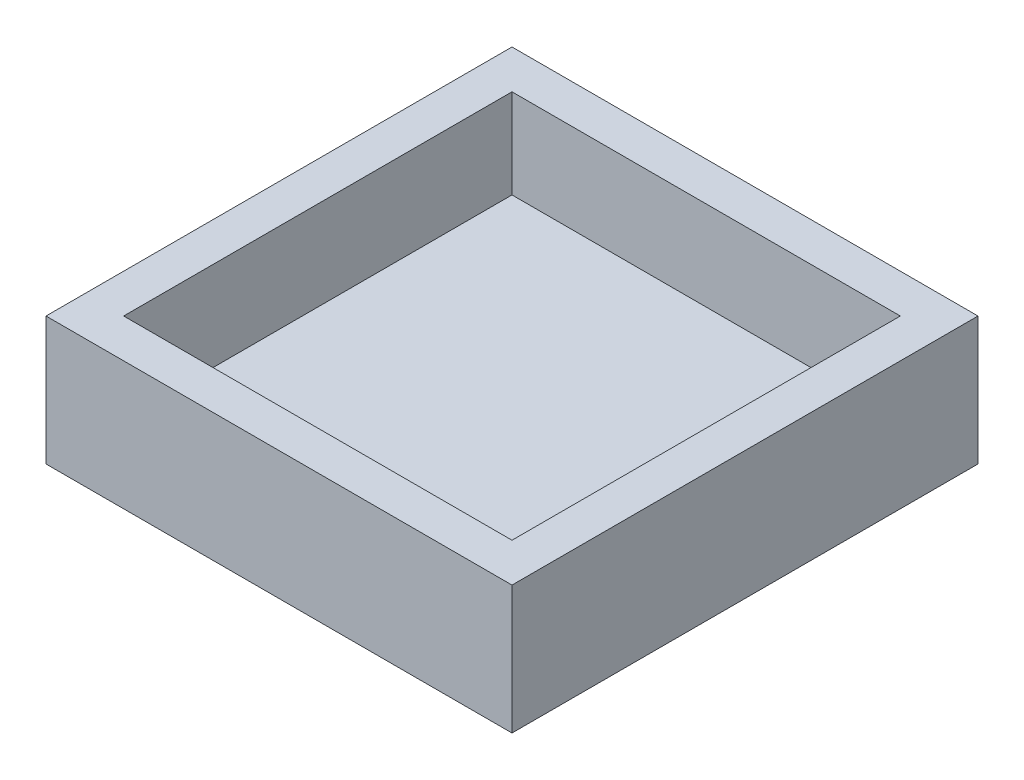
SolidWorks part; units mm, degrees
ref_plane "Front Plane" through (0, 0, 0) normal (0, 0, 1) x (1, 0, 0)
ref_plane "Top Plane" through (0, 0, 0) normal (0, 1, 0) x (1, 0, 0)
ref_plane "Right Plane" through (0, 0, 0) normal (1, 0, 0) x (0, 0, -1)
sketch "Sketch2" plane through (0, 0, 0) normal (0, 1, 0) x (1, 0, 0)
  line L1 (-54.6108, 53.5329) -> (65.3892, 53.5329)
  line L2 (-54.6108, 53.5329) -> (-54.6108, -66.4671)
  line L3 (-54.6108, -66.4671) -> (65.3892, -66.4671)
  line L4 (65.3892, 53.5329) -> (65.3892, -66.4671)
  dimension "D1" = 120
  dimension "D2" = 120
extrude "Boss-Extrude1" add sketch "Sketch2" along normal blind 33
shell "Shell1" thickness 10
